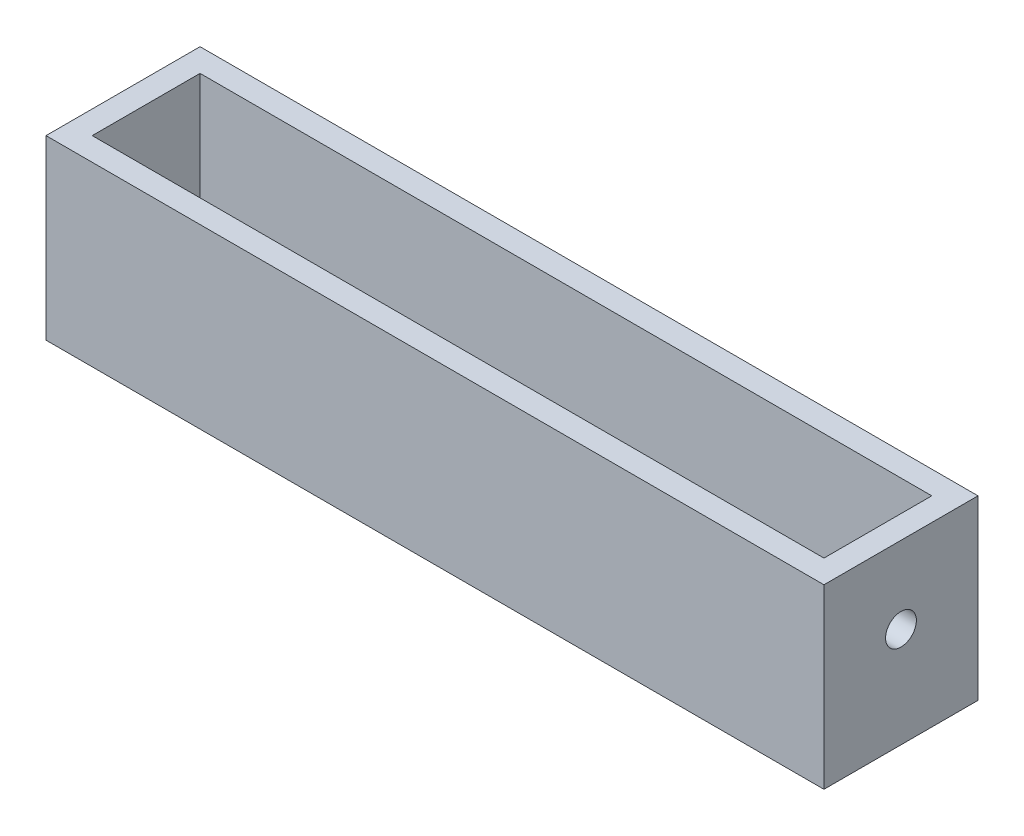
SolidWorks part; units mm, degrees
ref_plane "前视基准面" through (0, 0, 0) normal (0, 0, 1) x (1, 0, 0)
ref_plane "上视基准面" through (0, 0, 0) normal (0, 1, 0) x (1, 0, 0)
ref_plane "右视基准面" through (0, 0, 0) normal (1, 0, 0) x (0, 0, -1)
sketch "草图1" plane through (0, 0, 0) normal (0, 1, 0) x (1, 0, 0)
  line L0 (-50.5, 0) -> (-37.5, 0)
  line L1 (-50.5, -10) -> (50.5, -10)
  line L2 (-50.5, -10) -> (-50.5, 10)
  line L3 (-50.5, 10) -> (50.5, 10)
  line L4 (50.5, -10) -> (50.5, 10)
  line L5 (-50.5, -10) -> (50.5, 10) construction
  line L6 (-50.5, 10) -> (50.5, -10) construction
  line L7 (50.5, 0) -> (37.5, 0)
  circle A0 centre (-37.5, 0) radius 4
  circle A1 centre (37.5, 0) radius 4
  point P0 (0, 0)
  dimension "D1" = 101
  dimension "D2" = 20
extrude "凸台-拉伸1" add sketch "草图1" along normal blind 3
sketch "草图2" plane through (-50.5, 0, 0) normal (-1, 0, 0) x (0, 0, 1)
  line L0 (-10, 3) -> (-10, 23)
  line L1 (-10, 23) -> (10, 23)
  line L2 (10, 23) -> (10, 3)
  line L3 (0, 23) -> (0, 13)
  circle A0 centre (0, 13) radius 2
extrude "凸台-拉伸2" add sketch "草图2" against normal blind 3
sketch "草图3" plane through (50.5, 0, 0) normal (1, 0, 0) x (0, 0, -1)
  line L0 (-10, 3) -> (-10, 23)
  line L1 (-10, 23) -> (10, 23)
  line L2 (10, 23) -> (10, 3)
  line L3 (10, 3) -> (-10, 3)
  circle A0 centre (0, 13) radius 2
extrude "凸台-拉伸3" add sketch "草图3" against normal blind 3
sketch "草图4" plane through (0, 0, 10) normal (0, 0, 1) x (1, 0, 0)
  line L0 (-47.5, 3) -> (-47.5, 23)
  line L1 (-47.5, 23) -> (47.5, 23)
  line L2 (47.5, 23) -> (47.5, 3)
  line L3 (47.5, 3) -> (-47.5, 3)
extrude "凸台-拉伸4" add sketch "草图4" against normal blind 3
sketch "草图5" plane through (0, 0, -10) normal (0, 0, -1) x (-1, 0, 0)
  line L0 (-47.5, 23) -> (-47.5, 3)
  line L1 (-47.5, 3) -> (47.5, 3)
  line L2 (47.5, 3) -> (47.5, 23)
  line L3 (47.5, 23) -> (-47.5, 23)
extrude "凸台-拉伸5" add sketch "草图5" against normal blind 3
